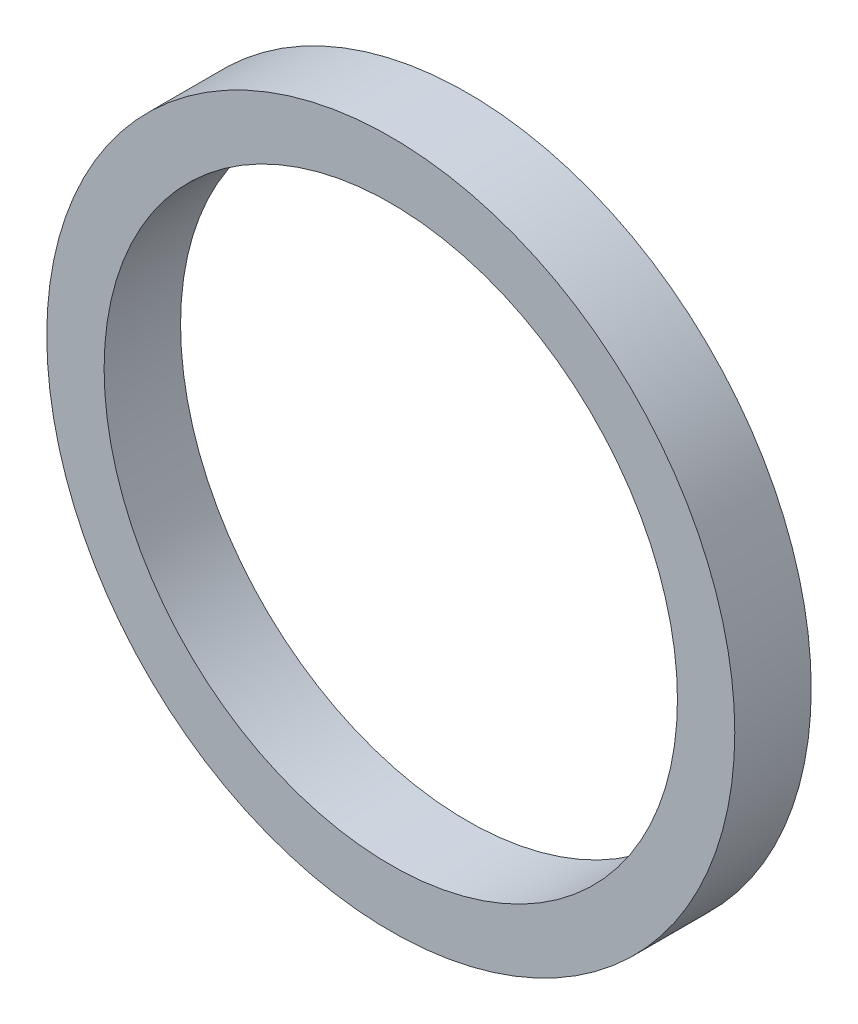
SolidWorks part; units mm, degrees
ref_plane "Front Plane" through (0, 0, 0) normal (0, 0, 1) x (1, 0, 0)
ref_plane "Top Plane" through (0, 0, 0) normal (0, 1, 0) x (1, 0, 0)
ref_plane "Right Plane" through (0, 0, 0) normal (1, 0, 0) x (0, 0, -1)
sketch "Sketch1" plane through (0, 0, 0) normal (0, 0, 1) x (1, 0, 0)
  circle A0 centre (0, 0) radius 2.3813
  circle A1 centre (0, 0) radius 2.8575
  dimension "D2" = 5.715
  dimension "D1" = 4.7625
extrude "Boss-Extrude1" add sketch "Sketch1" along normal blind 0.635
